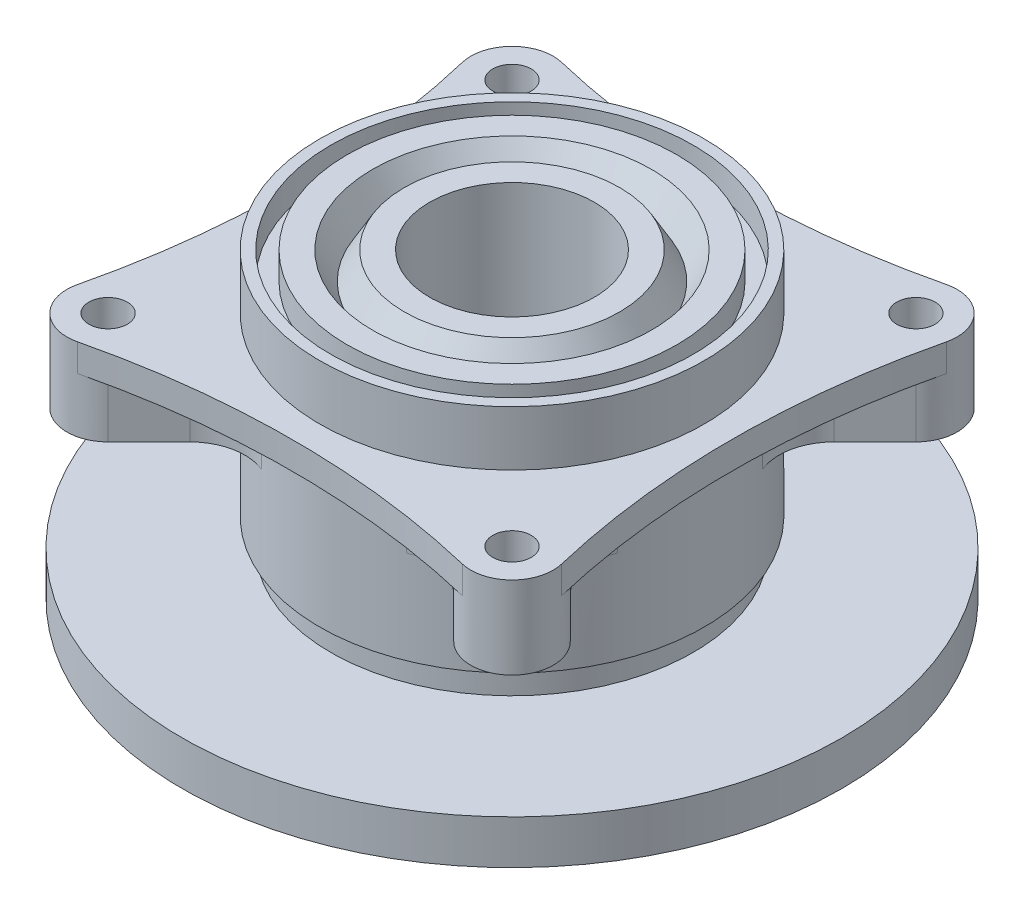
SolidWorks part; units mm, degrees
material "Alloy Steel"
ref_plane "Front Plane" through (0, 0, 0) normal (0, 0, 1) x (1, 0, 0)
ref_plane "Top Plane" through (0, 0, 0) normal (0, 1, 0) x (1, 0, 0)
ref_plane "Right Plane" through (0, 0, 0) normal (1, 0, 0) x (0, 0, -1)
sketch "Sketch1" plane through (0, 0, 0) normal (0, 0, 1) x (1, 0, 0)
  line L0 (0, 25.6125) -> (0, -25.6125) construction
  line L1 (15, 60) -> (15, 0)
  line L2 (15, 0) -> (30, 0)
  line L5 (31.7633, -10) -> (36, -10)
  line L6 (36, -10) -> (37.7633, 0)
  line L7 (37.7633, 0) -> (37.7633, 5)
  line L8 (37.7633, 5) -> (60, 5)
  line L9 (60, 5) -> (60, 13)
  line L10 (60, 13) -> (33, 13)
  line L16 (35, 18) -> (35, 60)
  line L21 (35, 60) -> (33, 60)
  line L22 (33, 60) -> (33, 55)
  line L23 (33, 55) -> (30, 55)
  line L24 (30, 55) -> (30, 60)
  line L25 (30, 60) -> (25.3868, 60)
  line L26 (25.3868, 60) -> (22.5, 55)
  line L27 (22.5, 55) -> (19.6132, 60)
  line L28 (19.6132, 60) -> (15, 60)
  line L29 (-11.0905, 0) -> (11.0905, 0) construction
  line L30 (22.5, 60.7521) -> (22.5, 49.2479) construction
  line L31 (31.7633, -10) -> (30, 0)
  line L33 (33, 13) -> (33, 18)
  line L34 (33, 18) -> (35, 18)
  point P4 (0, 0)
  point P37 (0, 0)
  point P43 (22.5, 55)
  dimension "D1" = 30
  dimension "D2" = 45
  dimension "D3" = 60
  dimension "D4" = 100
  dimension "D5" = 66
  dimension "D6" = 60
  dimension "D7" = 5
  dimension "D8" = 60
  dimension "D9" = 70
  dimension "D10" = 5
  dimension "D11" = 2
  dimension "D12" = 20
  dimension "D17" = 120
  dimension "D18" = 8
  dimension "D19" = 10
  dimension "D22" = 5
  dimension "D24" = 72
revolve "Revolve1" add sketch "Sketch1" angle 360 about L0
ref_plane "Plane1" through (0, 50, 0) normal (0, 1, 0) x (1, 0, 0)
sketch "Sketch3" plane through (0, 50, 0) normal (0, 1, 0) x (1, 0, 0)
  line L0 (0, 0) -> (36.7696, 36.7696) construction
  line L1 (-71.6409, 0) -> (71.6409, 0) construction
  arc A0 (44.0623, 35.0186) -> (35.0186, 44.0623) centre (36.7696, 36.7696) ccw
  arc A1 (35.0186, -44.0623) -> (44.0623, -35.0186) centre (36.7696, -36.7696) ccw
  arc A2 (-44.0623, -35.0186) -> (-35.0186, -44.0623) centre (-36.7696, -36.7696) ccw
  arc A3 (-35.0186, 44.0623) -> (-44.0623, 35.0186) centre (-36.7696, 36.7696) ccw
  arc A4 (44.0623, 35.0186) -> (44.0623, -35.0186) centre (189.9174, 0) ccw
  arc A5 (35.0186, -44.0623) -> (-35.0186, -44.0623) centre (0, -189.9174) ccw
  arc A6 (-44.0623, -35.0186) -> (-44.0623, 35.0186) centre (-189.9174, 0) ccw
  arc A7 (-35.0186, 44.0623) -> (35.0186, 44.0623) centre (0, 189.9174) ccw
  circle A8 centre (0, 0) radius 35
  circle A9 centre (0, 0) radius 35 construction
  point P5 (0, 0)
  point P16 (0, 0)
  point P29 (0, 0)
  dimension "D2" = 15
  dimension "D5" = 150
  dimension "D1" = 45
  dimension "D3" = 52
  dimension "D4" = 4
  dimension "D6" = 4
extrude "Boss-Extrude1" add sketch "Sketch3" against normal blind 5
sketch "Sketch4" plane through (0, 45, 0) normal (0, -1, 0) x (1, 0, 0)
  line L0 (29.4772, 18.8705) -> (42.0729, 31.4663)
  line L1 (0, 0) -> (36.7696, 36.7696) construction
  line L3 (18.8705, 29.4772) -> (31.4663, 42.0729)
  arc A0 (42.0729, 31.4663) -> (31.4663, 42.0729) centre (36.7696, 36.7696) ccw
  arc A1 (44.0623, 35.0186) -> (35.0186, 44.0623) centre (36.7696, 36.7696) ccw construction
  circle A2 centre (0, 0) radius 35 construction
  arc A3 (29.4772, 18.8705) -> (18.8705, 29.4772) centre (0, 0) ccw
extrude "Boss-Extrude3" add sketch "Sketch4" along normal blind 10
fillet "Fillet1" radius 10 2 edges at (29.4772, 40, 18.8705) (18.8705, 40, 29.4772)
sketch "Sketch5" plane through (0, 50, 0) normal (0, 1, 0) x (1, 0, 0)
  circle A0 centre (36.7696, -36.7696) radius 3.5
  dimension "D1" = 7
extrude "Cut-Extrude1" cut sketch "Sketch5" against normal up to next (15 mm away)
pattern_circular "CirPattern1" count 4 over 360 about axis through (0, 0, 0) along (0, 1, 0) of "Boss-Extrude3", "Fillet1", "Cut-Extrude1"
